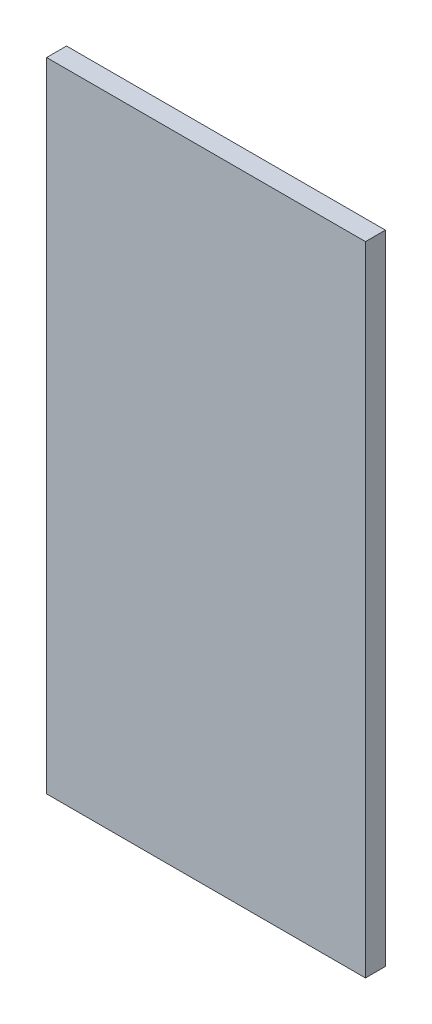
SolidWorks part; units mm, degrees
ref_plane "Front Plane" through (0, 0, 0) normal (0, 0, 1) x (1, 0, 0)
ref_plane "Top Plane" through (0, 0, 0) normal (0, 1, 0) x (1, 0, 0)
ref_plane "Right Plane" through (0, 0, 0) normal (1, 0, 0) x (0, 0, -1)
sketch "Sketch1" plane through (0, 0, 0) normal (0, 0, 1) x (1, 0, 0)
  line L1 (50.8, -101.6) -> (-50.8, -101.6)
  line L2 (50.8, -101.6) -> (50.8, 101.6)
  line L3 (50.8, 101.6) -> (-50.8, 101.6)
  line L4 (-50.8, -101.6) -> (-50.8, 101.6)
  line L5 (50.8, -101.6) -> (-50.8, 101.6) construction
  line L6 (50.8, 101.6) -> (-50.8, -101.6) construction
  point P0 (0, 0)
  dimension "D1" = 101.6
  dimension "D2" = 203.2
extrude "Boss-Extrude1" add sketch "Sketch1" along normal blind 6.35
